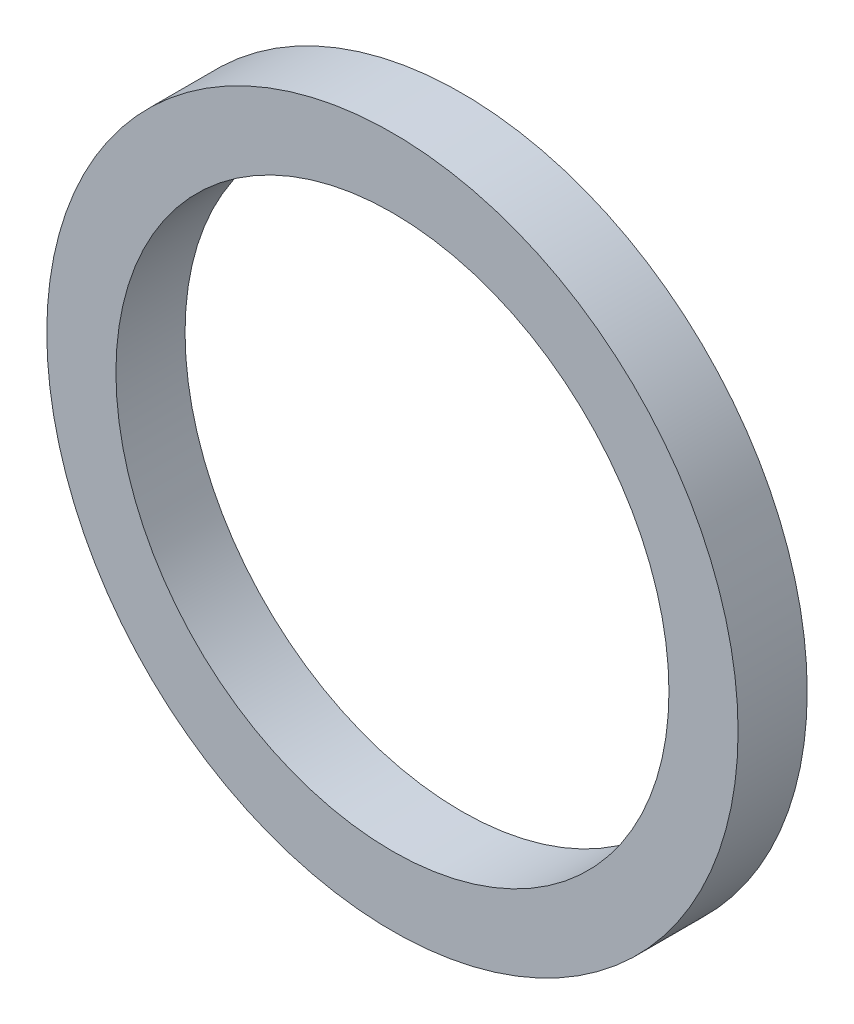
SolidWorks part; units mm, degrees
ref_plane "前视基准面" through (0, 0, 0) normal (0, 0, 1) x (1, 0, 0)
ref_plane "上视基准面" through (0, 0, 0) normal (0, 1, 0) x (1, 0, 0)
ref_plane "右视基准面" through (0, 0, 0) normal (1, 0, 0) x (0, 0, -1)
sketch "草图1" plane through (0, 0, 0) normal (0, 0, 1) x (1, 0, 0)
  circle A0 centre (0, 0) radius 50
  circle A1 centre (0, 0) radius 40
  dimension "D1" = 80
  dimension "D2" = 100
extrude "凸台-拉伸1" add sketch "草图1" along normal blind 10
